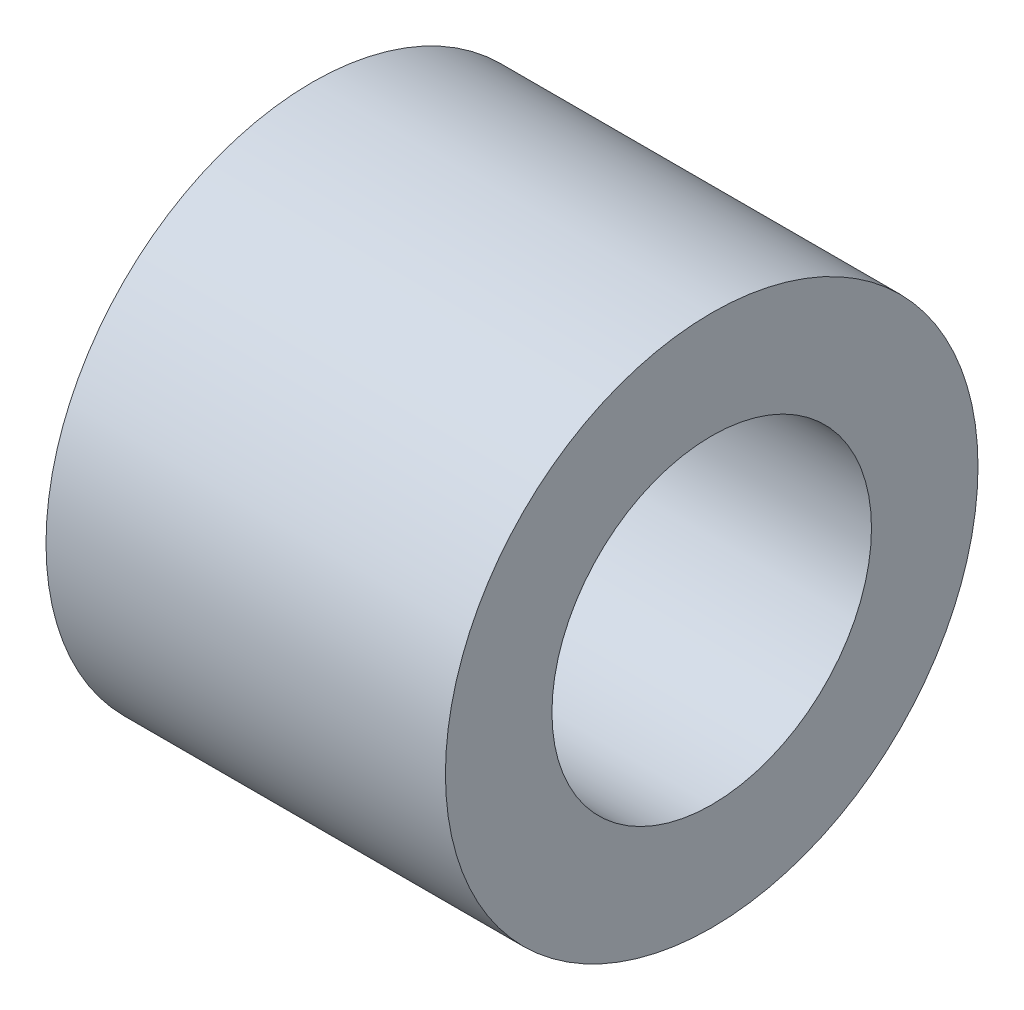
SolidWorks part; units mm, degrees
ref_plane "Front Plane" through (0, 0, 0) normal (0, 0, 1) x (1, 0, 0)
ref_plane "Top Plane" through (0, 0, 0) normal (0, 1, 0) x (1, 0, 0)
ref_plane "Right Plane" through (0, 0, 0) normal (1, 0, 0) x (0, 0, -1)
sketch "Sketch2" plane through (0, 0, 0) normal (1, 0, 0) x (0, 0, -1)
  circle A0 centre (0, 0) radius 12.7
  circle A1 centre (0, 0) radius 7.62
extrude "Boss-Extrude1" add sketch "Sketch2" along normal blind 19.05
ref_plane "Plane1" through (57.15, 0, 0) normal (1, 0, 0) x (0, 0, -1)
sketch "Sketch4" plane through (19.05, 0, 0) normal (1, 0, 0) x (0, 0, -1)
  line L0 (-7.62, 0) -> (-5.08, 0)
  line L1 (-5.08, 0) -> (-2.54, 0)
  line L2 (-2.54, 0) -> (0, 0)
  line L3 (0, 0) -> (2.54, 0)
  line L4 (2.54, 0) -> (5.08, 0)
  line L5 (5.08, 0) -> (7.62, 0)
  line L6 (-6.35, -6.3423) -> (-6.35, 6.3423) construction
  line L7 (-7.62, -6.3423) -> (-7.62, 6.3423)
  line L8 (-5.08, -6.3423) -> (-5.08, 6.3423)
  line L9 (-3.81, -8.5161) -> (-3.81, 8.5161) construction
  line L10 (-5.08, -8.5161) -> (-5.08, 8.5161)
  line L11 (-2.54, -8.5161) -> (-2.54, 8.5161)
  line L12 (-1.27, -10.0035) -> (-1.27, 10.0035) construction
  line L13 (-2.54, -10.0035) -> (-2.54, 10.0035)
  line L14 (0, -10.0035) -> (0, 10.0035)
  line L15 (1.27, -10.0035) -> (1.27, 10.0035) construction
  line L16 (0, -10.0035) -> (0, 10.0035)
  line L17 (2.54, -10.0035) -> (2.54, 10.0035)
  line L18 (3.81, -8.5161) -> (3.81, 8.5161) construction
  line L19 (2.54, -8.5161) -> (2.54, 8.5161)
  line L20 (5.08, -8.5161) -> (5.08, 8.5161)
  line L21 (6.35, -6.3423) -> (6.35, 6.3423) construction
  line L22 (5.08, -6.3423) -> (5.08, 6.3423)
  line L23 (7.62, -6.3423) -> (7.62, 6.3423)
  line L24 (-6.35, -5.5194) -> (-6.35, 5.5194) construction
  line L25 (-7.239, -5.5194) -> (-7.239, 5.5194)
  line L26 (-5.461, -5.5194) -> (-5.461, 5.5194)
  line L27 (-3.81, -5.5194) -> (-3.81, 5.5194) construction
  line L28 (-4.699, -5.5194) -> (-4.699, 5.5194)
  line L29 (-2.921, -5.5194) -> (-2.921, 5.5194)
  line L30 (-1.27, -5.5194) -> (-1.27, 5.5194) construction
  line L31 (-2.159, -5.5194) -> (-2.159, 5.5194)
  line L32 (-0.381, -5.5194) -> (-0.381, 5.5194)
  line L33 (1.27, -5.588) -> (1.27, 5.588) construction
  line L34 (0.381, -5.588) -> (0.381, 5.588)
  line L35 (2.159, -5.588) -> (2.159, 5.588)
  line L36 (3.81, 5.588) -> (3.81, -5.588) construction
  line L37 (4.699, 5.588) -> (4.699, -5.588)
  line L38 (2.921, 5.588) -> (2.921, -5.588)
  line L39 (6.35, 5.5194) -> (6.35, -5.5194) construction
  line L40 (7.239, 5.5194) -> (7.239, -5.5194)
  line L41 (5.461, 5.5194) -> (5.461, -5.5194)
  circle A0 centre (0, 0) radius 7.62
  arc A1 (-7.62, -6.3423) -> (-5.08, -6.3423) centre (-6.35, -6.3423) ccw
  arc A2 (-5.08, 6.3423) -> (-7.62, 6.3423) centre (-6.35, 6.3423) ccw
  arc A3 (-5.08, -8.5161) -> (-2.54, -8.5161) centre (-3.81, -8.5161) ccw
  arc A4 (-2.54, 8.5161) -> (-5.08, 8.5161) centre (-3.81, 8.5161) ccw
  arc A5 (-2.54, -10.0035) -> (0, -10.0035) centre (-1.27, -10.0035) ccw
  arc A6 (0, 10.0035) -> (-2.54, 10.0035) centre (-1.27, 10.0035) ccw
  arc A7 (0, -10.0035) -> (2.54, -10.0035) centre (1.27, -10.0035) ccw
  arc A8 (2.54, 10.0035) -> (0, 10.0035) centre (1.27, 10.0035) ccw
  arc A9 (2.54, -8.5161) -> (5.08, -8.5161) centre (3.81, -8.5161) ccw
  arc A10 (5.08, 8.5161) -> (2.54, 8.5161) centre (3.81, 8.5161) ccw
  arc A11 (5.08, -6.3423) -> (7.62, -6.3423) centre (6.35, -6.3423) ccw
  arc A12 (7.62, 6.3423) -> (5.08, 6.3423) centre (6.35, 6.3423) ccw
  arc A13 (-7.239, -5.5194) -> (-5.461, -5.5194) centre (-6.35, -5.5194) ccw
  arc A14 (-5.461, 5.5194) -> (-7.239, 5.5194) centre (-6.35, 5.5194) ccw
  arc A15 (-4.699, -5.5194) -> (-2.921, -5.5194) centre (-3.81, -5.5194) ccw
  arc A16 (-2.921, 5.5194) -> (-4.699, 5.5194) centre (-3.81, 5.5194) ccw
  arc A17 (-2.159, -5.5194) -> (-0.381, -5.5194) centre (-1.27, -5.5194) ccw
  arc A18 (-0.381, 5.5194) -> (-2.159, 5.5194) centre (-1.27, 5.5194) ccw
  arc A19 (0.381, -5.588) -> (2.159, -5.588) centre (1.27, -5.588) ccw
  arc A20 (2.159, 5.588) -> (0.381, 5.588) centre (1.27, 5.588) ccw
  arc A21 (4.699, 5.588) -> (2.921, 5.588) centre (3.81, 5.588) ccw
  arc A22 (2.921, -5.588) -> (4.699, -5.588) centre (3.81, -5.588) ccw
  arc A23 (7.239, 5.5194) -> (5.461, 5.5194) centre (6.35, 5.5194) ccw
  arc A24 (5.461, -5.5194) -> (7.239, -5.5194) centre (6.35, -5.5194) ccw
  point P12 (-6.35, 0)
  point P20 (-3.81, 0)
  point P27 (-1.27, 0)
  point P34 (1.27, 0)
  point P41 (3.81, 0)
  point P47 (6.35, 0)
  point P54 (-6.35, 0)
  point P62 (-3.81, 0)
  point P68 (-1.27, 0)
  point P76 (1.27, 0)
  point P82 (3.81, 0)
  point P90 (6.35, 0)
  dimension "D3" = 15.24
  dimension "D1" = 2.54
  dimension "D2" = 2.54
  dimension "D4" = 2.54
  dimension "D5" = 2.54
  dimension "D6" = 2.54
  dimension "D7" = 2.54
  dimension "D8" = 2.54
  dimension "D9" = 2.54
  dimension "D10" = 2.54
  dimension "D11" = 2.54
  dimension "D12" = 2.54
  dimension "D13" = 1.778
  dimension "D14" = 1.778
  dimension "D15" = 1.778
  dimension "D16" = 11.176
  dimension "D17" = 1.778
  dimension "D18" = 1.778
  dimension "D19" = 1.778
sketch "Sketch3" plane through (57.15, 0, 0) normal (1, 0, 0) x (0, 0, -1)
  line L0 (-82.55, 0) -> (82.55, 0)
  line L1 (-82.55, 12.7) -> (82.55, 12.7)
  line L2 (-82.55, 12.7) -> (-82.55, -12.7)
  line L3 (-82.55, -12.7) -> (82.55, -12.7)
  line L4 (82.55, 12.7) -> (82.55, -12.7)
  line L5 (-82.55, 12.7) -> (82.55, -12.7) construction
  line L6 (-82.55, -12.7) -> (82.55, 12.7) construction
  line L7 (-57.15, 0) -> (-54.61, 0)
  line L8 (-29.21, 0) -> (-26.67, 0)
  line L9 (0, 0) -> (0, -12.7)
  circle A0 centre (-69.85, 0) radius 12.7
  circle A1 centre (-41.91, 0) radius 12.7
  circle A2 centre (-13.97, 0) radius 12.7
  circle A3 centre (69.85, 0) radius 12.7
  circle A4 centre (41.91, 0) radius 12.7
  circle A5 centre (13.97, 0) radius 12.7
  point P0 (0, 0)
  dimension "D1" = 25.4
  dimension "D4" = 25.4
  dimension "D5" = 2.54
  dimension "D2" = 2.54
  dimension "D3" = 165.1
